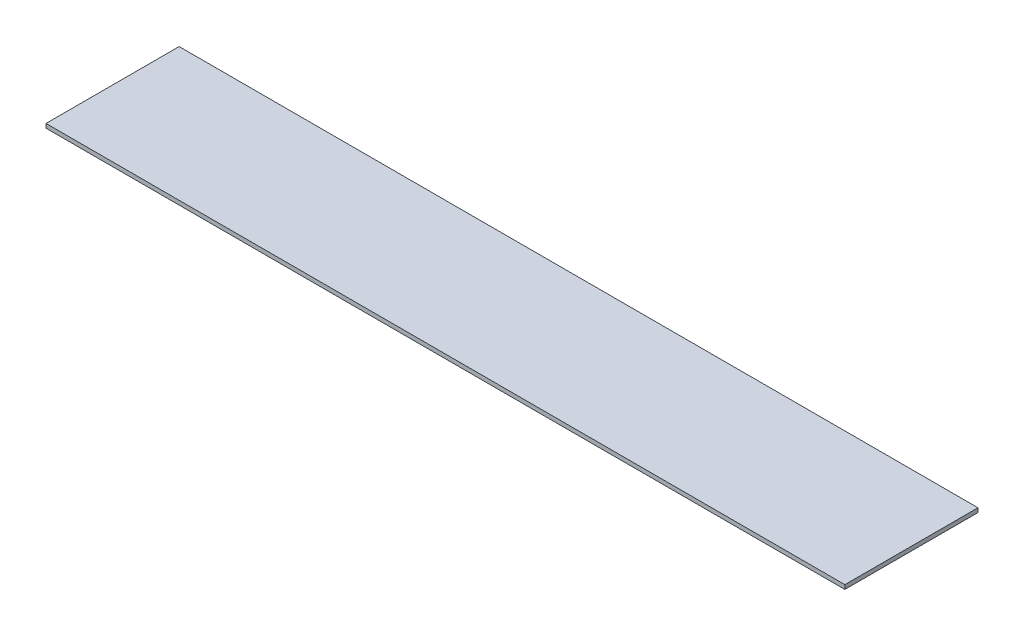
SolidWorks part; units mm, degrees
material "Nylon 6/10"
ref_plane "Front Plane" through (0, 0, 0) normal (0, 0, 1) x (1, 0, 0)
ref_plane "Top Plane" through (0, 0, 0) normal (0, 1, 0) x (1, 0, 0)
ref_plane "Right Plane" through (0, 0, 0) normal (1, 0, 0) x (0, 0, -1)
sketch "Sketch1" plane through (0, -80.2624, 0) normal (0, -1, 0) x (1, 0, 0)
  line L2 (0, 0) -> (609.6, 0)
  line L3 (0, 0) -> (0, 101.6)
  line L4 (0, 101.6) -> (609.6, 101.6)
  line L5 (609.6, 0) -> (609.6, 101.6)
  dimension "D2" = 609.6
  dimension "D1" = 101.6
extrude "Boss-Extrude1" add sketch "Sketch1" along normal blind 3.175
